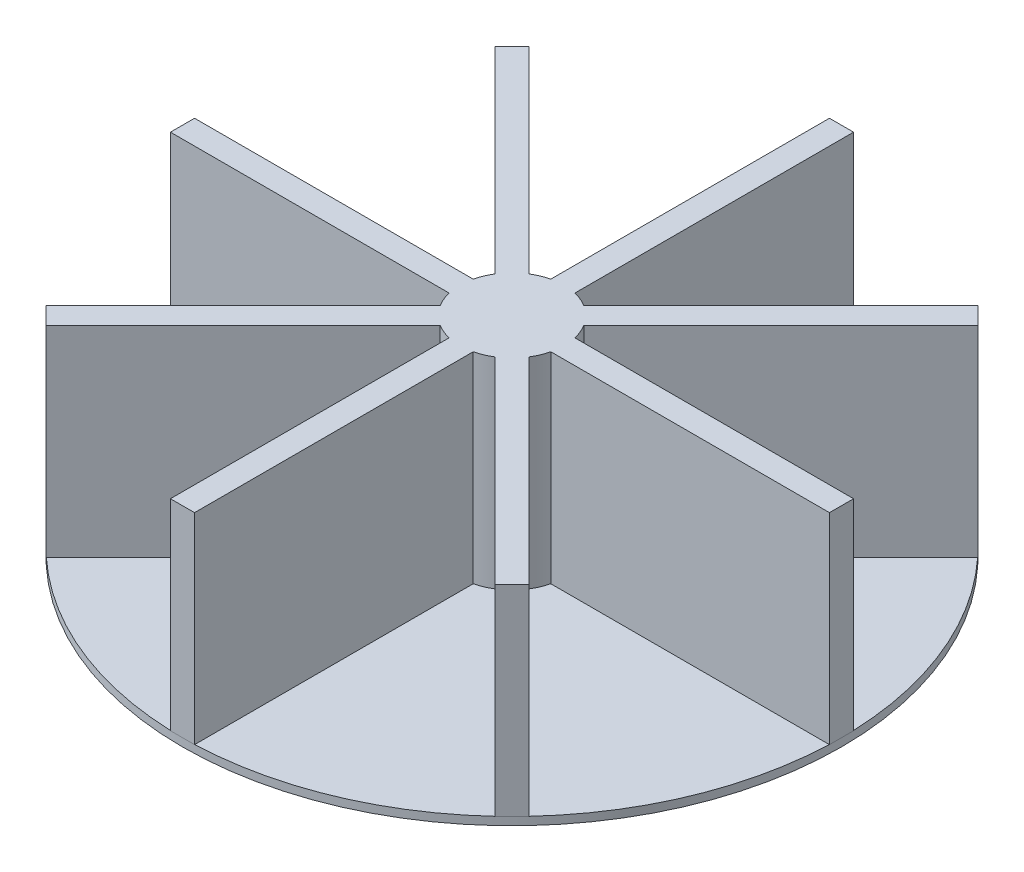
SolidWorks part; units mm, degrees
ref_plane "Front Plane" through (0, 0, 0) normal (0, 0, 1) x (1, 0, 0)
ref_plane "Top Plane" through (0, 0, 0) normal (0, 1, 0) x (1, 0, 0)
ref_plane "Right Plane" through (0, 0, 0) normal (1, 0, 0) x (0, 0, -1)
sketch "Sketch1" plane through (0, 0, 0) normal (0, 1, 0) x (1, 0, 0)
  circle A0 centre (0, 0) radius 41
  dimension "D1" = 82
extrude "Boss-Extrude1" add sketch "Sketch1" along normal blind 1
sketch "Sketch5" plane through (0, 1, 0) normal (0, 1, 0) x (1, 0, 0)
  line L0 (0, -41) -> (0, 41) construction
  line L1 (-41, 0) -> (41, 0) construction
  circle A0 centre (0, 0) radius 41 construction
sketch "Sketch6" plane through (0, 1, 0) normal (0, 1, 0) x (1, 0, 0)
  line L29 (-1.5, 0) -> (1.5, 0)
  line L30 (-1.5, 0) -> (-1.5, -41)
  line L31 (-1.5, -41) -> (1.5, -41)
  line L32 (1.5, 0) -> (1.5, -41)
  point P32 (0, 0)
  dimension "D1" = 3
  dimension "D2" = 1.5
  dimension "D3" = 41
extrude "Boss-Extrude7" add sketch "Sketch6" along normal blind 25
sketch "Sketch7" plane through (0, 0, 0) normal (0, -1, 0) x (1, 0, 0)
  circle A0 centre (0, 0) radius 6
extrude "Boss-Extrude8" add sketch "Sketch7" against normal blind 24
sketch "Sketch10" plane through (0, 0, 0) normal (0, -1, 0) x (-1, 0, 0)
  line L25 (0, 0) -> (0.2889, 53.175) construction
  line L26 (4.0389, 53.175) -> (-3.4611, 53.175) construction
  line L27 (0, 0) -> (-28.8335, 29.1484) construction
  line L29 (0, 0) -> (-15.484, 37.9637) construction
  line L30 (-3.143, 11.6778) -> (-5.9208, 10.5448)
  line L31 (-5.9208, 10.5448) -> (-7.8091, 15.1746)
  line L32 (-7.8091, 15.1746) -> (-5.0313, 16.3075)
  line L33 (-5.0313, 16.3075) -> (-3.143, 11.6778)
  circle A1 centre (0, 0) radius 41 construction
  point P29 (0, 0)
  point P58 (0, 0)
  dimension "D1" = 45
  dimension "D2" = 22.5
  dimension "D3" = 3
  dimension "D4" = 5
  dimension "D5" = 1.5
  dimension "D6" = 12
sketch "Sketch9" plane through (0, 26, 0) normal (0, 1, 0) x (1, 0, 0)
  circle A0 centre (0, 0) radius 6
extrude "Cut-Extrude3" cut sketch "Sketch9" against normal blind 5
pattern_circular "CirPattern1" count 8 over 360 about axis through (0, 0, 0) along (0, 1, 0) of "Boss-Extrude7"
sketch "Sketch11" plane through (0, 26, 0) normal (0, 1, 0) x (1, 0, 0)
  circle A0 centre (0, 0) radius 6
extrude "Cut-Extrude5" cut sketch "Sketch11" against normal blind 6
extrude "Boss-Extrude9" add sketch "Sketch10" along normal blind 2
pattern_circular "CirPattern2" count 8 over 360 about axis through (0, 0, 0) along (0, 1, 0) of "Boss-Extrude9"
fillet "Fillet1" radius 1 32 edges at (4.5319, -2, -11.1113) (6.865, -2, -12.8597) (6.4202, -2, -15.7411) (4.0871, -2, -13.9927) (11.0614, -2, -4.6524) (13.9475, -2, -4.2389) (15.6704, -2, -6.5908) (12.7844, -2, -7.0043) (11.1113, -2, 4.5319) (12.8597, -2, 6.865) (15.7411, -2, 6.4202) (13.9927, -2, 4.0871) (4.6524, -2, 11.0614) (4.2389, -2, 13.9475) (6.5908, -2, 15.6704) (7.0043, -2, 12.7844) (-4.5319, -2, 11.1113) (-6.865, -2, 12.8597) (-6.4202, -2, 15.7411) (-4.0871, -2, 13.9927) (-11.0614, -2, 4.6524) (-13.9475, -2, 4.2389) (-15.6704, -2, 6.5908) (-12.7844, -2, 7.0043) (-11.1113, -2, -4.5319) (-12.8597, -2, -6.865) (-15.7411, -2, -6.4202) (-13.9927, -2, -4.0871) (-4.6524, -2, -11.0614) (-4.2389, -2, -13.9475) (-6.5908, -2, -15.6704) (-7.0043, -2, -12.7844)
sketch "Sketch13" plane through (0, 20, 0) normal (0, 1, 0) x (1, 0, 0)
  circle A0 centre (0, 0) radius 6.5
  dimension "D1" = 13
extrude "Boss-Extrude17" add sketch "Sketch13" along normal blind 6
sketch "Sketch15" plane through (0, 0, 0) normal (0, -1, 0) x (1, 0, 0)
  circle A0 centre (0, 0) radius 6
  dimension "D1" = 12
sketch "Sketch16" plane through (0, 26, 0) normal (0, 1, 0) x (1, 0, 0)
  circle A0 centre (0, 0) radius 6.5
  circle A1 centre (0, 0) radius 6
extrude "Boss-Extrude18" add sketch "Sketch16" against normal blind 25
extrude "Boss-Extrude19" add sketch "Sketch15" along normal blind 3
sketch "Sketch17" plane through (0, -3, 0) normal (0, -1, 0) x (1, 0, 0)
  circle A0 centre (0, 0) radius 3.075
  dimension "D1" = 6.15
extrude "Cut-Extrude10" cut sketch "Sketch17" against normal blind 5
